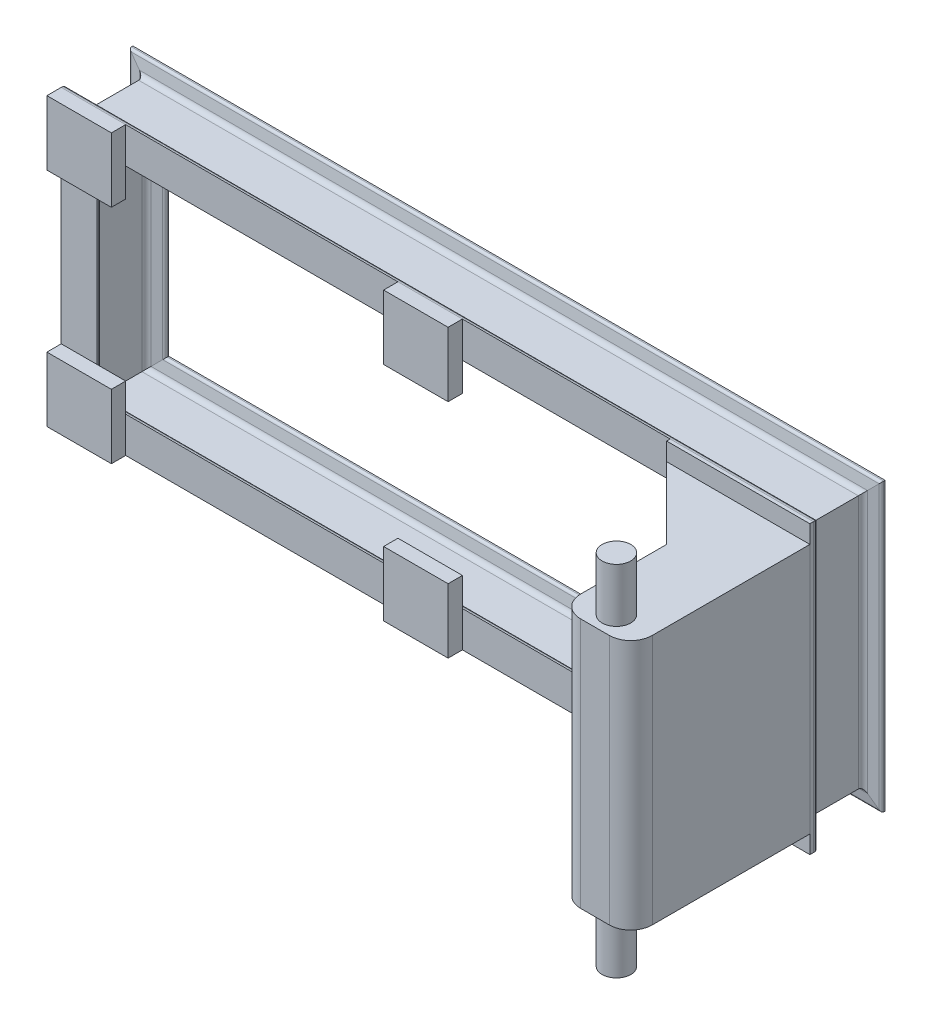
SolidWorks part; units mm, degrees
ref_plane "Front Plane" through (0, 0, 0) normal (0, 0, 1) x (1, 0, 0)
ref_plane "Top Plane" through (0, 0, 0) normal (0, 1, 0) x (1, 0, 0)
ref_plane "Right Plane" through (0, 0, 0) normal (1, 0, 0) x (0, 0, -1)
sketch "Sketch1" plane through (0, 0, 0) normal (0, 0, 1) x (1, 0, 0)
  line L1 (500, 175) -> (-500, 175)
  line L2 (500, 175) -> (500, -175)
  line L3 (500, -175) -> (-500, -175)
  line L4 (-500, 175) -> (-500, -175)
  line L5 (500, 175) -> (-500, -175) construction
  line L6 (500, -175) -> (-500, 175) construction
  point P0 (0, 0)
  dimension "D1" = 350
  dimension "D2" = 1000
other "Sb beam - configured 100 X 8(1)"
ref_plane "Plane1" through (500, 175, 0) normal (-1, 0, 0) x (0, -1, 0)
sketch "Sketch16" plane through (500, 175, 0) normal (-1, 0, 0) x (0, -1, 0)
  line L0 (-25, -50) -> (-25, -48.0607)
  line L1 (-22.0754, -44.6083) -> (-8.0991, -42.2787)
  line L2 (-2.25, -35.374) -> (-2.25, 35.374)
  line L3 (-8.0991, 42.2787) -> (-22.0754, 44.6083)
  line L4 (-25, 48.0607) -> (-25, 50)
  line L5 (-25, 50) -> (25, 50)
  line L6 (25, 50) -> (25, 48.0607)
  line L7 (22.0754, 44.6083) -> (8.0991, 42.2787)
  line L8 (2.25, 35.374) -> (2.25, -35.374)
  line L9 (8.0991, -42.2787) -> (22.0754, -44.6083)
  line L10 (25, -48.0607) -> (25, -50)
  line L11 (25, -50) -> (-25, -50)
  line L15 (-2.25, 0) -> (2.25, 0) construction
  arc A0 (-8.0991, -42.2787) -> (-2.25, -35.374) centre (-9.25, -35.374) ccw
  arc A1 (-2.25, 35.374) -> (-8.0991, 42.2787) centre (-9.25, 35.374) ccw
  arc A2 (8.0991, 42.2787) -> (2.25, 35.374) centre (9.25, 35.374) ccw
  arc A3 (2.25, -35.374) -> (8.0991, -42.2787) centre (9.25, -35.374) ccw
  arc A4 (-22.0754, 44.6083) -> (-25, 48.0607) centre (-21.5, 48.0607) cw
  arc A5 (22.0754, 44.6083) -> (25, 48.0607) centre (21.5, 48.0607) ccw
  arc A6 (-25, -48.0607) -> (-22.0754, -44.6083) centre (-21.5, -48.0607) cw
  arc A7 (25, -48.0607) -> (22.0754, -44.6083) centre (21.5, -48.0607) ccw
  point P1 (0, 50)
  point P8 (0, -50)
  point P21 (0, 0)
  point P34 (0, 0)
  dimension "RI" = 7
  dimension "D3" = 3.5
  dimension "BF" = 50
  dimension "D2" = 9.463
  dimension "DEPTH" = 100
  dimension "TW" = 4.5
  dimension "D1" = 70.748
sketch "Sketch17" plane through (0, 0, 50) normal (0, 0, 1) x (1, 0, 0)
  line L0 (-525, 200) -> (525, 200) construction
  line L1 (-525, 200) -> (-435, 200)
  line L2 (-525, 200) -> (-525, 110)
  line L3 (-525, 110) -> (-435, 110)
  line L4 (-435, 200) -> (-435, 110)
  line L5 (-525, -200) -> (-435, -200)
  line L6 (-525, -200) -> (-525, -110)
  line L7 (-525, -110) -> (-435, -110)
  line L8 (-435, -200) -> (-435, -110)
  line L9 (35, 200) -> (-55, 200)
  line L10 (35, 200) -> (35, 110)
  line L11 (35, 110) -> (-55, 110)
  line L12 (-55, 200) -> (-55, 110)
  line L13 (525, -200) -> (-525, -200) construction
  line L14 (35, -200) -> (-55, -200)
  line L15 (35, -200) -> (35, -110)
  line L16 (35, -110) -> (-55, -110)
  line L17 (-55, -200) -> (-55, -110)
  dimension "D1" = 90
  dimension "D2" = 90
  dimension "D3" = 90
  dimension "D4" = 90
  dimension "D5" = 35
extrude "Boss-Extrude1" add sketch "Sketch17" along normal blind 20 separate body
sketch "Sketch18" plane through (0, 0, 50) normal (0, 0, 1) x (1, 0, 0)
  line L0 (525, -200) -> (-525, -200) construction
  line L1 (525, 200) -> (325, 200)
  line L2 (525, 200) -> (525, -200)
  line L3 (525, -200) -> (325, -200)
  line L4 (325, 200) -> (325, -200)
  dimension "D1" = 200
extrude "Boss-Extrude2" add sketch "Sketch18" along normal blind 5 separate body
sketch "Sketch20" plane through (0, 0, 0) normal (0, 1, 0) x (1, 0, 0)
  line L0 (525, -55) -> (325, -55)
  line L1 (325, -55) -> (425, -155)
  line L2 (425, -155) -> (425, -305)
  line L3 (425, -305) -> (525, -305)
  line L4 (525, -305) -> (525, -55)
  dimension "D1" = 250
  dimension "D2" = 100
  dimension "D3" = 150
extrude "Boss-Extrude3" add sketch "Sketch20" along normal mid plane 350 separate body
sketch "Sketch21" plane through (0, 0, 0) normal (0, 1, 0) x (1, 0, 0)
  line L0 (425, -305) -> (525, -305) construction
  line L1 (425, -155) -> (425, -305) construction
  circle A0 centre (475, -275) radius 20
  dimension "D1" = 40
  dimension "D2" = 30
  dimension "D3" = 50
extrude "Boss-Extrude4" add sketch "Sketch21" along normal mid plane 500
fillet "Fillet1" radius 30 2 edges at (425, 0, 305) (525, 0, 305)
